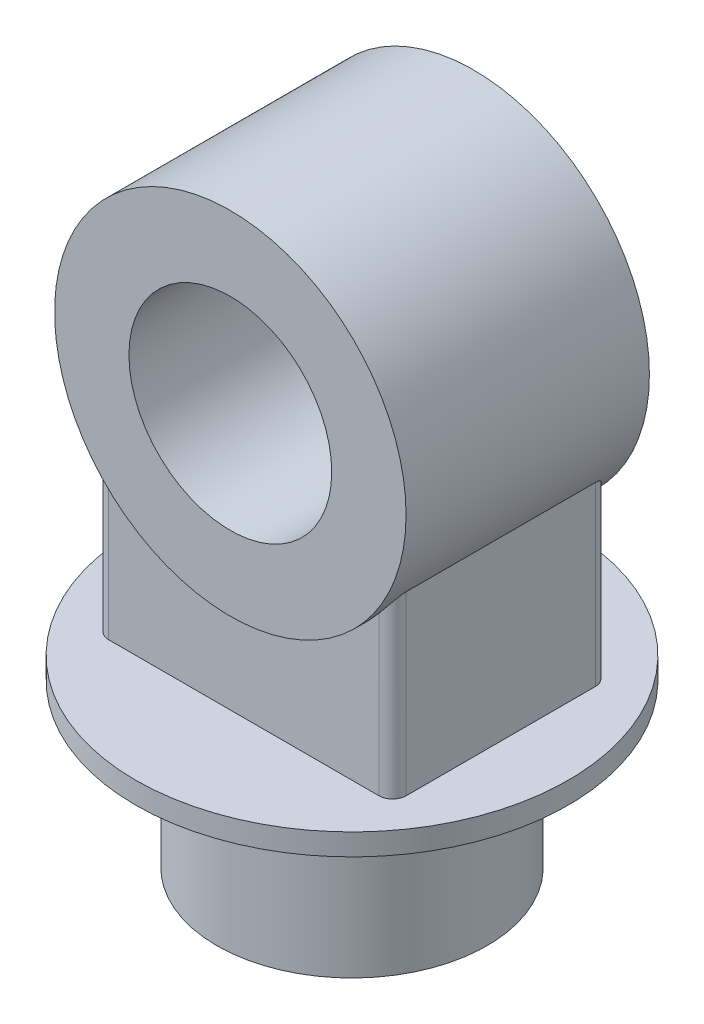
SolidWorks part; units mm, degrees
ref_plane "Front Plane" through (0, 0, 0) normal (0, 0, 1) x (1, 0, 0)
ref_plane "Top Plane" through (0, 0, 0) normal (0, 1, 0) x (1, 0, 0)
ref_plane "Right Plane" through (0, 0, 0) normal (1, 0, 0) x (0, 0, -1)
sketch "Sketch1" plane through (0, 0, 0) normal (0, 1, 0) x (1, 0, 0)
  circle A0 centre (0, 0) radius 100
  dimension "D1" = 200
extrude "Boss-Extrude1" add sketch "Sketch1" along normal blind 120
sketch "Sketch2" plane through (0, 120, 0) normal (0, 1, 0) x (1, 0, 0)
  circle A0 centre (0, 0) radius 160
  dimension "D1" = 320
extrude "Boss-Extrude3" add sketch "Sketch2" along normal blind 16
sketch "Sketch3" plane through (0, 0, 0) normal (0, 0, 1) x (1, 0, 0)
  line L0 (160, 136) -> (-160, 136) construction
  circle A0 centre (0, 336) radius 75
  circle A1 centre (0, 336) radius 130
  dimension "D1" = 150
  dimension "D2" = 260
  dimension "D3" = 200
extrude "Boss-Extrude4" add sketch "Sketch3" along normal mid plane 180 separate body
sketch "Sketch4" plane through (0, 136, 0) normal (0, 1, 0) x (1, 0, 0)
  line L1 (-110, -80) -> (110, -80)
  line L2 (-110, -80) -> (-110, 80)
  line L3 (-110, 80) -> (110, 80)
  line L4 (110, -80) -> (110, 80)
  line L5 (-110, -80) -> (110, 80) construction
  line L6 (-110, 80) -> (110, -80) construction
  point P0 (0, 0)
  dimension "D1" = 160
  dimension "D2" = 220
extrude "Boss-Extrude5" add sketch "Sketch4" along normal up to next
fillet "Fillet1" radius 10 4 edges at (110, 201.359, -80) (110, 201.359, 80) (-110, 201.359, -80) (-110, 201.359, 80)
